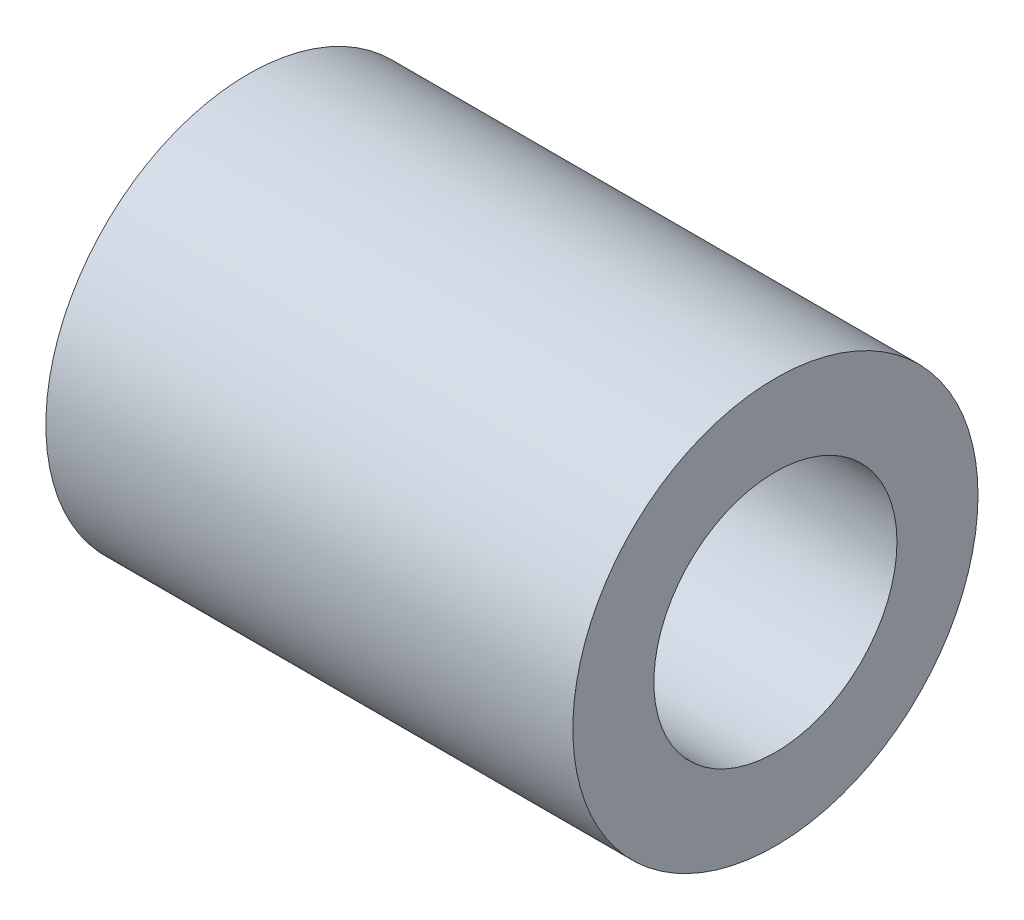
SolidWorks part; units mm, degrees
material "Nylon 101"
ref_plane "Front Plane" through (0, 0, 0) normal (0, 0, 1) x (1, 0, 0)
ref_plane "Top Plane" through (0, 0, 0) normal (0, 1, 0) x (1, 0, 0)
ref_plane "Right Plane" through (0, 0, 0) normal (1, 0, 0) x (0, 0, -1)
sketch "Sketch1" plane through (0, 0, 0) normal (1, 0, 0) x (0, 0, -1)
  circle A0 centre (0, 0) radius 4.7625
  circle A1 centre (0, 0) radius 7.9375
  dimension "D1" = 9.525
  dimension "D2" = 15.875
extrude "Boss-Extrude1" add sketch "Sketch1" along normal blind 20.6502
